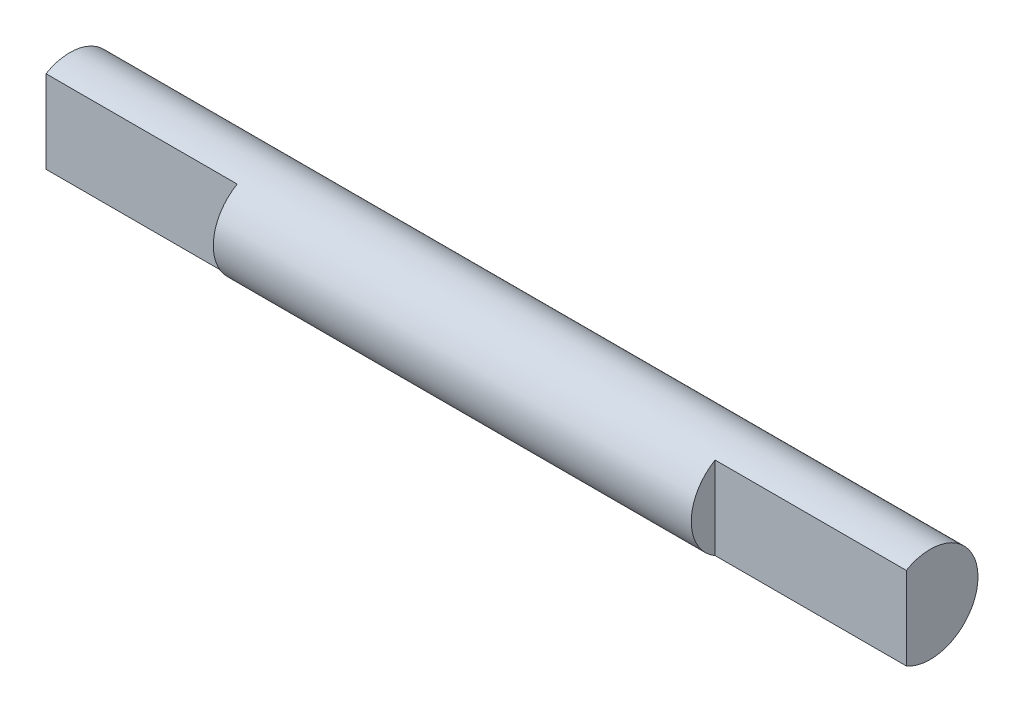
SolidWorks part; units mm, degrees
ref_plane "Front Plane" through (0, 0, 0) normal (0, 0, 1) x (1, 0, 0)
ref_plane "Top Plane" through (0, 0, 0) normal (0, 1, 0) x (1, 0, 0)
ref_plane "Right Plane" through (0, 0, 0) normal (1, 0, 0) x (0, 0, -1)
sketch "Sketch1" plane through (0, 0, 0) normal (1, 0, 0) x (0, 0, -1)
  circle A0 centre (0, 0) radius 12.7
  dimension "D1" = 25.4
extrude "Boss-Extrude1" add sketch "Sketch1" along normal mid plane 127
sketch "Sketch2" plane through (63.5, 0, 0) normal (1, 0, 0) x (0, 0, -1)
  line L0 (-6.35, 10.9985) -> (-6.35, -10.9985)
  circle A0 centre (0, 0) radius 12.7
  circle A1 centre (0, 0) radius 12.7 construction
  circle M3 centre (0, 0) radius 12.7
  dimension "D1" = 19.05
extrude "Boss-Extrude2" add sketch "Sketch2" along normal blind 50.8 contours L0 M3
mirror "Mirror1" about plane through (0, 0, 0) normal (1, 0, 0) of "Boss-Extrude2"
